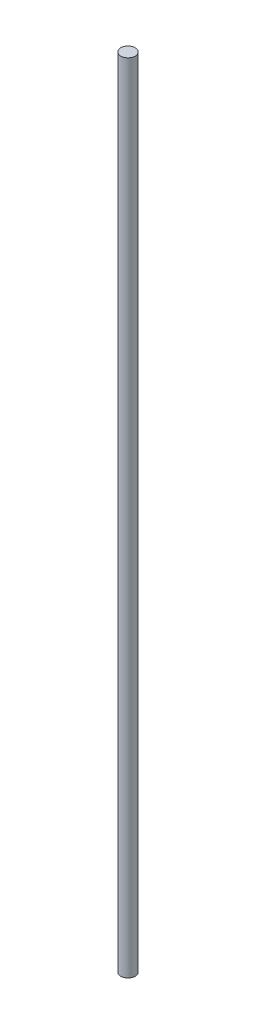
SolidWorks part; units mm, degrees
ref_plane "Front Plane" through (0, 0, 0) normal (0, 0, 1) x (1, 0, 0)
ref_plane "Top Plane" through (0, 0, 0) normal (0, 1, 0) x (1, 0, 0)
ref_plane "Right Plane" through (0, 0, 0) normal (1, 0, 0) x (0, 0, -1)
sketch "Sketch1" plane through (0, 0, 0) normal (0, 1, 0) x (1, 0, 0)
  circle A0 centre (0, 0) radius 6
extrude "Boss-Extrude1" add sketch "Sketch1" along normal blind 660
